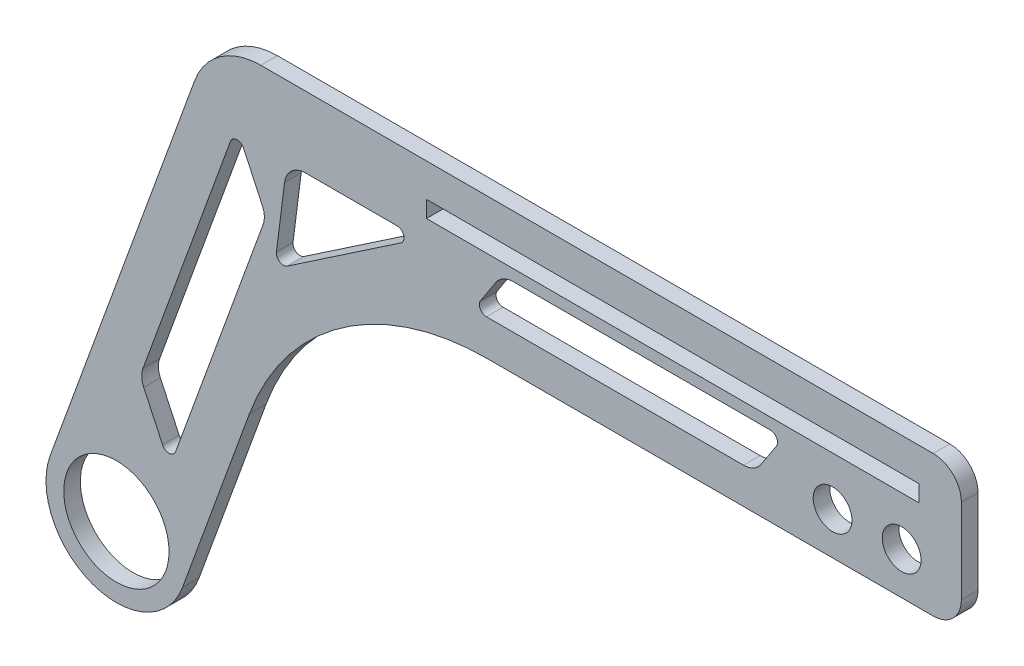
SolidWorks part; units mm, degrees
material "Acrylic (Medium-high impact)"
ref_plane "Front Plane" through (0, 0, 0) normal (0, 0, 1) x (1, 0, 0)
ref_plane "Top Plane" through (0, 0, 0) normal (0, 1, 0) x (1, 0, 0)
ref_plane "Right Plane" through (0, 0, 0) normal (1, 0, 0) x (0, 0, -1)
sketch "Sketch1" plane through (0, 0, 0) normal (0, 0, 1) x (1, 0, 0)
  line L0 (-11.9341, 4.3437) -> (14.1278, 75.9482)
  line L1 (26.0619, 84.3046) -> (152.4742, 84.3046)
  line L2 (11.9341, -4.3437) -> (24.0053, 28.8217)
  line L3 (66.9681, 58.9046) -> (152.4742, 58.9046)
  line L4 (0, 0) -> (26.0619, 71.6046) construction
  line L5 (0, 0) -> (165.1, 0) construction
  line L6 (26.0619, 71.6046) -> (152.4742, 71.6046) construction
  line L7 (165.1, 0) -> (152.4742, 71.6046) construction
  line L8 (152.4742, 58.9046) -> (152.4742, 84.3046)
  line L10 (55.9542, 78.3046) -> (144.8542, 78.3046)
  line L11 (55.9542, 78.3046) -> (55.9542, 75.3046)
  line L12 (55.9542, 75.3046) -> (144.8542, 75.3046)
  line L13 (144.8542, 78.3046) -> (144.8542, 75.3046)
  arc A0 (-11.9341, 4.3437) -> (11.9341, -4.3437) centre (0, 0) ccw
  arc A1 (24.0053, 28.8217) -> (66.9681, 58.9046) centre (66.9681, 13.1846) cw
  circle A3 centre (0, 0) radius 9.5025
  arc A4 (26.0619, 84.3046) -> (14.1278, 75.9482) centre (26.0619, 71.6046) ccw
  arc A5 (152.4742, 58.9046) -> (152.4742, 84.3046) centre (152.4742, 71.6046) ccw construction
  arc A7 (14.458, 32.2967) -> (66.9681, 69.0646) centre (66.9681, 13.1846) cw construction
  dimension "D3" = 25.4
  dimension "D4" = 76.2
  dimension "D6" = 19.005
  dimension "D7" = 25.4
  dimension "D8" = 45.72
  dimension "D1" = 70
  dimension "D2" = 80
  dimension "D5" = 165.1
  dimension "D9" = 3
  dimension "D10" = 88.9
  dimension "D11" = 6
  dimension "D12" = 7.62
  dimension "D16" = 10.16
extrude "Boss-Extrude1" add sketch "Sketch1" along normal blind 3
sketch "Sketch2" plane through (0, 0, 3) normal (0, 0, 1) x (1, 0, 0)
  line L0 (9.6335, 13.3395) -> (4.2662, 24.8496)
  line L1 (4.2662, 24.8496) -> (21.6408, 72.586)
  line L2 (21.6408, 72.586) -> (27.0081, 61.0759)
  line L3 (27.0081, 61.0759) -> (9.6335, 13.3395)
  line L4 (9.6335, 13.3395) -> (6.596, 14.7637)
  line L5 (6.9498, 19.0946) -> (24.3245, 66.8309) construction
  line L6 (0, 0) -> (26.0619, 71.6046) construction
  dimension "D1" = 50.8
  dimension "D2" = 12.7
  dimension "D3" = 20.32
  dimension "D4" = 45
extrude "Cut-Extrude1" cut sketch "Sketch2" against normal through all contours L3 L2 L1 L0
sketch "Sketch3" plane through (0, 0, 3) normal (0, 0, 1) x (1, 0, 0)
  line L0 (30.7777, 71.5124) -> (28.5239, 53.7476)
  line L1 (28.5239, 53.7476) -> (54.7734, 71.5124)
  line L2 (54.7734, 71.5124) -> (30.7777, 71.5124)
  line L3 (64.4364, 65.363) -> (69.5668, 73.2723)
  line L4 (69.5668, 73.2723) -> (120.3668, 73.2723)
  line L5 (120.3668, 73.2723) -> (115.2364, 65.363)
  line L6 (115.2364, 65.363) -> (64.4364, 65.363)
  dimension "D1" = 8.4823
  dimension "D2" = 50.8
extrude "Cut-Extrude2" cut sketch "Sketch3" against normal blind 127
fillet "Fillet1" radius 3.81 5 edges at (115.2364, 65.363, 1.5) (69.5668, 73.2723, 1.5) (30.7777, 71.5124, 1.5) (27.0081, 61.0759, 1.5) (4.2662, 24.8496, 1.5)
fillet "Fillet2" radius 1.27 6 edges at (120.3668, 73.2723, 1.5) (64.4364, 65.363, 1.5) (54.7734, 71.5124, 1.5) (28.5239, 53.7476, 1.5) (9.6335, 13.3395, 1.5) (21.6408, 72.586, 1.5)
fillet "Fillet3" radius 5.08 2 edges at (152.4742, 58.9046, 1.5) (152.4742, 84.3046, 1.5)
sketch "Sketch4" plane through (0, 0, 3) normal (0, 0, 1) x (1, 0, 0)
  circle A0 centre (141.6942, 66.5142) radius 3.5025
  circle A1 centre (129.2354, 66.5142) radius 3.5025
  dimension "D1" = 7.005
extrude "Cut-Extrude3" cut sketch "Sketch4" against normal blind 16.002
